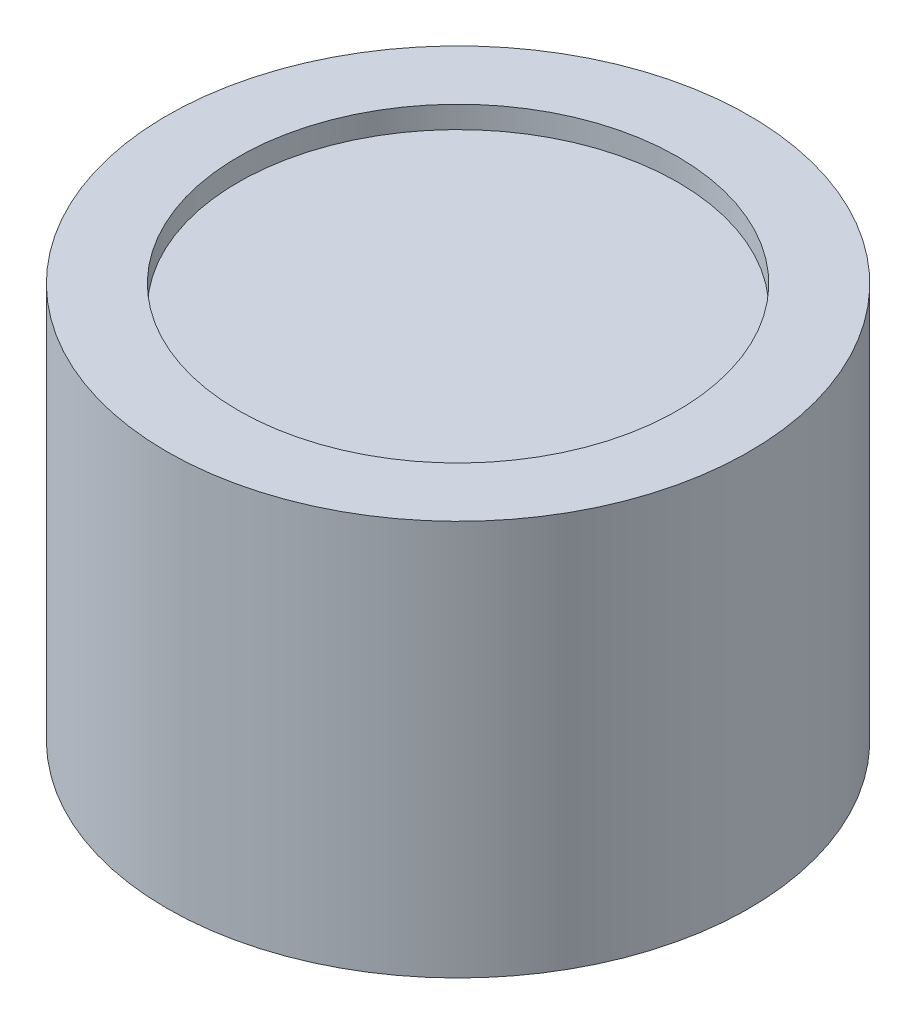
SolidWorks part; units mm, degrees
ref_plane "Front Plane" through (0, 0, 0) normal (0, 0, 1) x (1, 0, 0)
ref_plane "Top Plane" through (0, 0, 0) normal (0, 1, 0) x (1, 0, 0)
ref_plane "Right Plane" through (0, 0, 0) normal (1, 0, 0) x (0, 0, -1)
sketch "Sketch1" plane through (0, 0, 0) normal (0, 1, 0) x (1, 0, 0)
  circle A1 centre (0, 0) radius 13.25
extrude "Boss-Extrude1" add sketch "Sketch1" along normal blind 35
sketch "Sketch7" plane through (0, 0, 0) normal (0, -1, 0) x (1, 0, 0)
  circle A0 centre (0, 0) radius 10
extrude "Cut-Extrude4" cut sketch "Sketch7" against normal blind 8 contours A0
sketch "Sketch10" plane through (0, 8, 0) normal (0, -1, 0) x (1, 0, 0)
  circle A0 centre (0, 0) radius 3.485
extrude "Boss-Extrude3" add sketch "Sketch10" along normal blind 4 contours A0
sketch "Sketch11" plane through (0, 4, 0) normal (0, -1, 0) x (1, 0, 0)
  line L0 (1.124, -1.1618) -> (-1.124, -1.1618)
  arc A4 (1.124, -1.1618) -> (-1.124, -1.1618) centre (0, 0) ccw
  point P5 (0, -1.1618)
  point P6 (0.083, 0)
extrude "Cut-Extrude5" cut sketch "Sketch11" against normal blind 8.75
sketch "Sketch13" plane through (0, 35, 0) normal (0, 1, 0) x (1, 0, 0)
  circle A0 centre (0, 0) radius 10
extrude "Cut-Extrude6" cut sketch "Sketch13" against normal blind 18
sketch "Sketch14" plane through (0, 35, 0) normal (0, 1, 0) x (1, 0, 0)
  circle A0 centre (0, 0) radius 13.25
extrude "Cut-Extrude7" cut sketch "Sketch14" against normal blind 17
